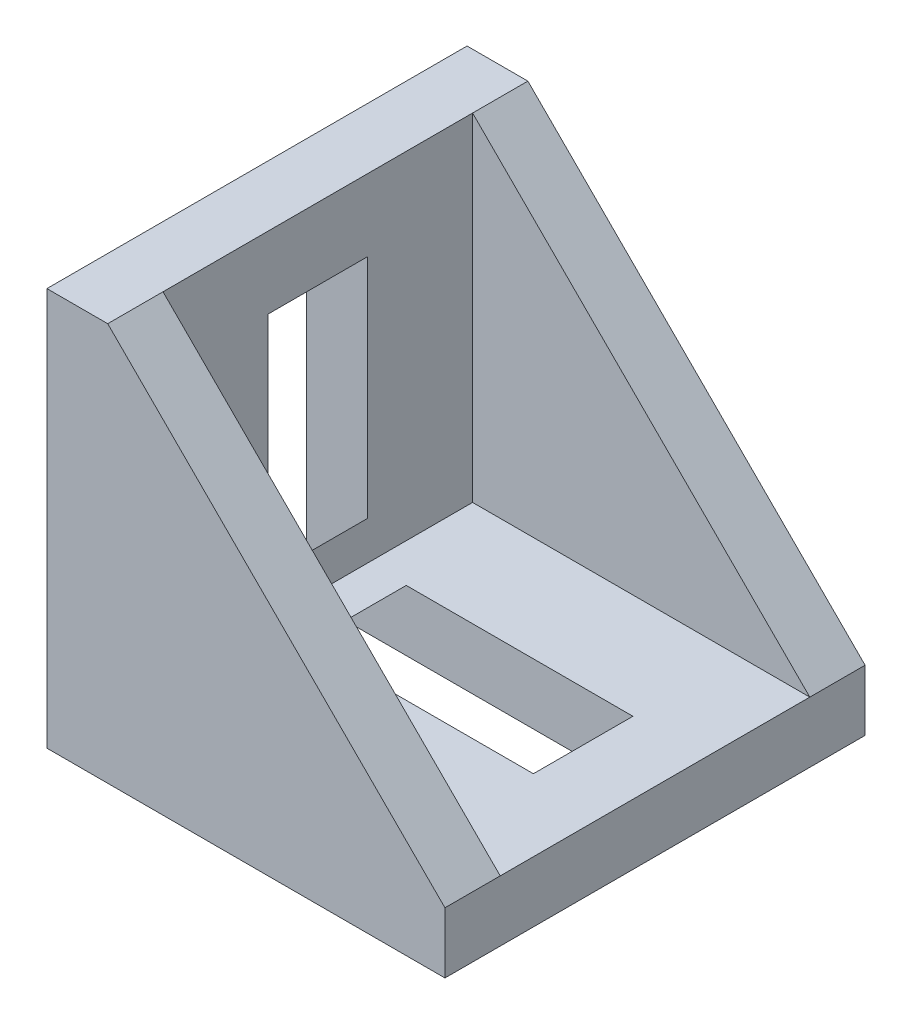
SolidWorks part; units mm, degrees
ref_plane "Front Plane" through (0, 0, 0) normal (0, 0, 1) x (1, 0, 0)
ref_plane "Top Plane" through (0, 0, 0) normal (0, 1, 0) x (1, 0, 0)
ref_plane "Right Plane" through (0, 0, 0) normal (1, 0, 0) x (0, 0, -1)
sketch "Sketch1" plane through (0, 0, 0) normal (0, 0, 1) x (1, 0, 0)
  line L0 (0, 0) -> (0, 36)
  line L1 (36, 5.5) -> (5.5, 36)
  line L4 (5.5, 36) -> (0, 36)
  line L5 (36, 0) -> (0, 0)
  line L7 (36, 5.5) -> (36, 0)
  dimension "D" = 5.5
  dimension "C" = 36
  dimension "B" = 36
extrude "Boss-Extrude1" add sketch "Sketch1" along normal mid plane 38
sketch "Sketch2" plane through (0, 0, 0) normal (0, 0, 1) x (1, 0, 0)
  line L0 (5.5, 36) -> (5.5, 5.5)
  line L1 (5.5, 5.5) -> (36, 5.5)
  line L2 (5.5, 36) -> (36, 5.5)
extrude "Cut-Extrude1" cut sketch "Sketch2" against normal mid plane 28
sketch "Sketch3" plane through (0, 0, 0) normal (0, 0, 1) x (1, 0, 0)
  line L0 (36, 5.5) -> (5.5, 36) construction
  line L1 (0, 29.5) -> (5.5, 29.5)
  line L2 (0, 29.5) -> (0, 3.5)
  line L3 (0, 3.5) -> (5.5, 9)
  line L4 (5.5, 29.5) -> (5.5, 9)
  line L5 (9, 5.5) -> (29.5, 5.5)
  line L6 (9, 5.5) -> (3.5, 0)
  line L7 (3.5, 0) -> (29.5, 0)
  line L8 (29.5, 5.5) -> (29.5, 0)
  line L10 (36, 0) -> (0, 0) construction
  line L11 (0, 0) -> (0, 36) construction
  dimension "D1" = 29.5
  dimension "D2" = 20.5
  dimension "D3" = 29.5
  dimension "D4" = 20.5
extrude "Cut-Extrude2" cut sketch "Sketch3" against normal mid plane 9
sketch "Sketch4" plane through (0, 0, 0) normal (0, 0, 1) x (1, 0, 0)
  line L0 (0, 36) -> (0, 0) construction
  line L1 (1.2115, 2.3429) -> (0, 1.2348) construction
  line L2 (0.7148, -2.5) -> (-0.2011, -1.5697)
  line L3 (0, 3.5355) -> (-2.5, 0.7148)
  line L4 (-2.5, 0.7148) -> (-1.5697, -0.2011)
  line L5 (-1.5697, -0.2011) -> (0, 1.2348)
  line L6 (0, 1.2348) -> (0, 3.5355)
  line L7 (-0.2011, -1.5697) -> (1.2348, 0)
  line L8 (0, 0) -> (0, 36) construction
  line L9 (-2.0348, 0.2568) -> (0, 2.3239) construction
  line L10 (1.2348, 0) -> (3.5355, 0)
  line L11 (3.5355, 0) -> (0.7148, -2.5)
  line L12 (0, 35.3) -> (0, 32.9992)
  line L13 (0, 32.9992) -> (-1.5697, 31.5634)
  line L14 (-1.5697, 31.5634) -> (-2.5, 32.4792)
  line L15 (-2.5, 32.4792) -> (0, 35.3)
  line L16 (-2.0348, 32.0213) -> (0, 34.0884) construction
  line L17 (0, 34.0884) -> (0.6057, 34.7037) construction
  line L18 (36, 5.5) -> (5.5, 36) construction
  line L19 (20.75, 20.75) -> (0, 0) construction
  line L20 (0, 35.3) -> (1.2115, 34.1074) construction
  line L21 (0, 32.9992) -> (1.2115, 34.1074) construction
  line L22 (0, 3.5355) -> (1.2115, 2.3429) construction
  line L23 (32.9992, 0) -> (31.5634, -1.5697)
  line L24 (0.6057, 2.9392) -> (0, 2.3239) construction
  line L25 (31.5634, -1.5697) -> (32.4792, -2.5)
  line L26 (35.3, 0) -> (32.9992, 0)
  line L27 (32.4792, -2.5) -> (35.3, 0)
  line L28 (-2.5, 0.7148) -> (-2.5, 32.4792) construction
  dimension "D1" = 1.7
  dimension "D2" = 5
  dimension "D3" = 6
  dimension "D4" = 1.6001
  dimension "D5" = 0.7
  dimension "D6" = 2.5
  dimension "D7" = 1.2445
extrude "Boss-Extrude2" add sketch "Sketch4" along normal mid plane 8
